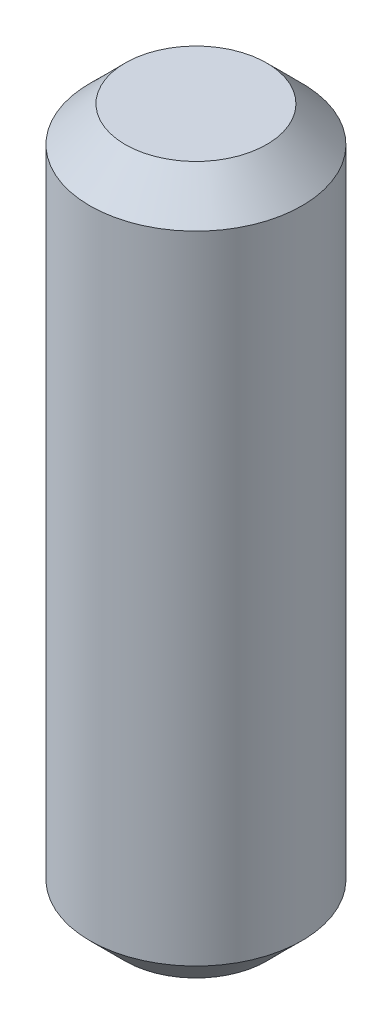
SolidWorks part; units mm, degrees
material "普通碳钢"
ref_plane "前视基准面" through (0, 0, 0) normal (0, 0, 1) x (1, 0, 0)
ref_plane "上视基准面" through (0, 0, 0) normal (0, 1, 0) x (1, 0, 0)
ref_plane "右视基准面" through (0, 0, 0) normal (1, 0, 0) x (0, 0, -1)
other "Configuration Table"
sketch "草图1" plane through (0, 0, 0) normal (0, 1, 0) x (1, 0, 0)
  circle A0 centre (0, 0) radius 1.5
  dimension "D1" = 3
extrude "凸台-拉伸1" add sketch "草图1" along normal mid plane 10
chamfer "倒角1" distance 0.5 angle 45 2 edges at (0, -5, 1.5) (0, 5, 1.5)
